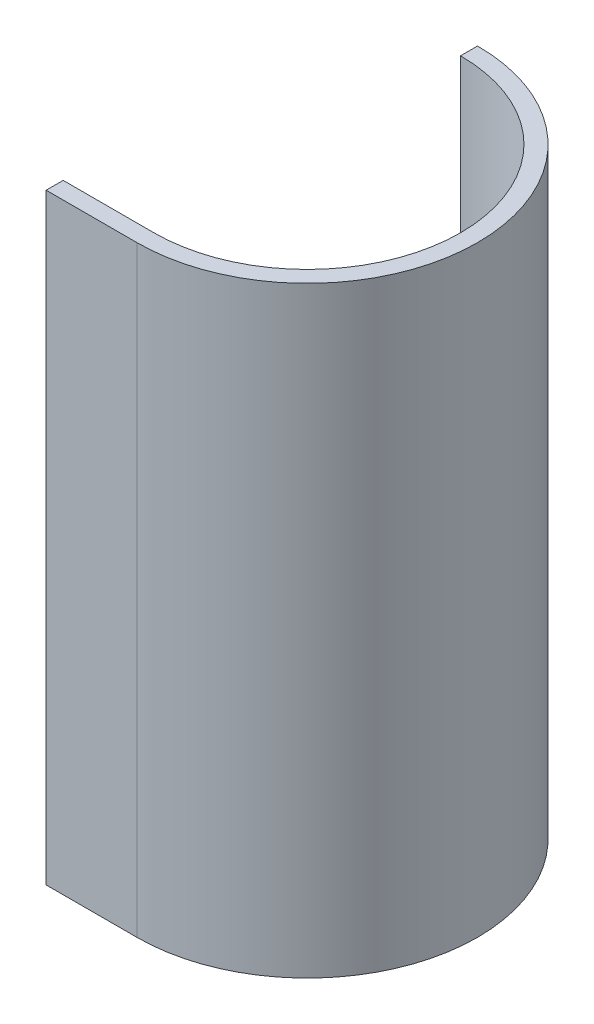
SolidWorks part; units mm, degrees
material "ABS PC"
ref_plane "Front Plane" through (0, 0, 0) normal (0, 0, 1) x (1, 0, 0)
ref_plane "Top Plane" through (0, 0, 0) normal (0, 1, 0) x (1, 0, 0)
ref_plane "Right Plane" through (0, 0, 0) normal (1, 0, 0) x (0, 0, -1)
sketch "Sketch1" plane through (0, 0, 0) normal (0, 1, 0) x (1, 0, 0)
  line L1 (0, 15) -> (0, 13.5)
  line L2 (0, -13.5) -> (-8, -13.5)
  line L3 (-8, -13.5) -> (-8, -15)
  line L4 (-8, -15) -> (0, -15)
  arc A0 (0, -13.5) -> (0, 13.5) centre (0, 0) ccw
  arc A1 (0, -15) -> (0, 15) centre (0, 0) ccw
  dimension "D1" = 13.5
  dimension "D2" = 15
  dimension "D3" = 8
extrude "Boss-Extrude1" add sketch "Sketch1" along normal blind 53
